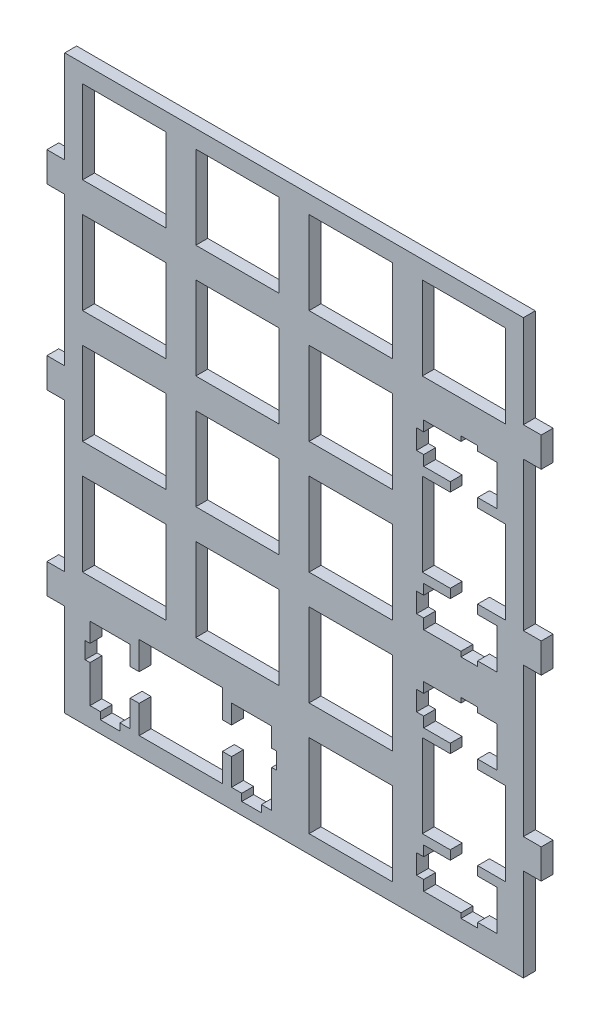
SolidWorks part; units mm, degrees
ref_plane "前视基准面" through (0, 0, 0) normal (0, 0, 1) x (1, 0, 0)
ref_plane "上视基准面" through (0, 0, 0) normal (0, 1, 0) x (1, 0, 0)
ref_plane "右视基准面" through (0, 0, 0) normal (1, 0, 0) x (0, 0, -1)
other "Configuration Table"
sketch "Model" plane through (0, 0, 0) normal (0, 0, 1) x (1, 0, 0)
  line L0 (12.1447, 16.7831) -> (12.1447, 12.0826)
  line L1 (12.1447, 12.0826) -> (10.6192, 12.0826)
  line L2 (10.6192, 12.0826) -> (10.6192, 15.3128)
  line L3 (10.6192, 15.3128) -> (3.8695, 15.3128)
  line L4 (3.8695, 15.3128) -> (3.8695, 12.0826)
  line L5 (3.8695, 12.0826) -> (3.0441, 12.0826)
  line L6 (3.0441, 12.0826) -> (3.0441, 9.2838)
  line L7 (3.0441, 9.2838) -> (3.8695, 9.2838)
  line L8 (3.8695, 9.2838) -> (3.8695, 3.0138)
  line L9 (3.8695, 3.0138) -> (5.5948, 3.0138)
  line L10 (5.5948, 3.0138) -> (5.5948, 1.8135)
  line L11 (5.5948, 1.8135) -> (8.8939, 1.8135)
  line L12 (8.8939, 1.8135) -> (8.8939, 3.0138)
  line L13 (8.8939, 3.0138) -> (10.6192, 3.0138)
  line L14 (10.6192, 3.0138) -> (10.6192, 7.4827)
  line L15 (10.6192, 7.4827) -> (12.1447, 7.4827)
  line L16 (12.1447, 7.4827) -> (12.1447, 2.7836)
  line L17 (12.1447, 2.7836) -> (26.1441, 2.7836)
  line L18 (26.1441, 2.7836) -> (26.1441, 7.4827)
  line L19 (26.1441, 7.4827) -> (27.6696, 7.4827)
  line L20 (27.6696, 7.4827) -> (27.6696, 3.0138)
  line L21 (27.6696, 3.0138) -> (29.3949, 3.0138)
  line L22 (29.3949, 3.0138) -> (29.3949, 1.8135)
  line L23 (29.3949, 1.8135) -> (32.694, 1.8135)
  line L24 (32.694, 1.8135) -> (32.694, 3.0138)
  line L25 (32.694, 3.0138) -> (34.4193, 3.0138)
  line L26 (34.4193, 3.0138) -> (34.4193, 9.2838)
  line L27 (34.4193, 9.2838) -> (35.2447, 9.2838)
  line L28 (35.2447, 9.2838) -> (35.2447, 12.0826)
  line L29 (35.2447, 12.0826) -> (34.4193, 12.0826)
  line L30 (34.4193, 12.0826) -> (34.4193, 15.3128)
  line L31 (34.4193, 15.3128) -> (27.6696, 15.3128)
  line L32 (27.6696, 15.3128) -> (27.6696, 12.0826)
  line L33 (27.6696, 12.0826) -> (26.1441, 12.0826)
  line L34 (26.1441, 12.0826) -> (26.1441, 16.7831)
  line L35 (26.1441, 16.7831) -> (12.1447, 16.7831)
  line L36 (40.7197, 16.7831) -> (54.719, 16.7831)
  line L37 (54.719, 16.7831) -> (54.719, 2.7836)
  line L38 (54.719, 2.7836) -> (40.7197, 2.7836)
  line L39 (40.7197, 2.7836) -> (40.7197, 16.7831)
  line L40 (66.27, 35.4087) -> (66.27, 34.5833)
  line L41 (66.27, 34.5833) -> (59.9997, 34.5833)
  line L42 (59.9997, 34.5833) -> (59.9997, 32.8579)
  line L43 (59.9997, 32.8579) -> (58.7996, 32.8579)
  line L44 (58.7996, 32.8579) -> (58.7996, 29.5589)
  line L45 (58.7996, 29.5589) -> (59.9997, 29.5589)
  line L46 (59.9997, 29.5589) -> (59.9997, 27.8336)
  line L47 (59.9997, 27.8336) -> (64.4701, 27.8336)
  line L48 (64.4701, 27.8336) -> (64.4701, 26.3081)
  line L49 (64.4701, 26.3081) -> (59.7697, 26.3081)
  line L50 (59.7697, 26.3081) -> (59.7697, 12.3086)
  line L51 (59.7697, 12.3086) -> (64.4701, 12.3086)
  line L52 (64.4701, 12.3086) -> (64.4701, 10.7831)
  line L53 (64.4701, 10.7831) -> (59.9997, 10.7831)
  line L54 (59.9997, 10.7831) -> (59.9997, 9.0579)
  line L55 (59.9997, 9.0579) -> (58.7996, 9.0579)
  line L56 (58.7996, 9.0579) -> (58.7996, 5.7588)
  line L57 (58.7996, 5.7588) -> (59.9997, 5.7588)
  line L58 (59.9997, 5.7588) -> (59.9997, 4.0335)
  line L59 (59.9997, 4.0335) -> (66.27, 4.0335)
  line L60 (66.27, 4.0335) -> (66.27, 3.2081)
  line L61 (66.27, 3.2081) -> (69.07, 3.2081)
  line L62 (69.07, 3.2081) -> (69.07, 4.0335)
  line L63 (69.07, 4.0335) -> (72.3, 4.0335)
  line L64 (72.3, 4.0335) -> (72.3, 10.7831)
  line L65 (72.3, 10.7831) -> (69.07, 10.7831)
  line L66 (69.07, 10.7831) -> (69.07, 12.3086)
  line L67 (69.07, 12.3086) -> (73.769, 12.3086)
  line L68 (73.769, 12.3086) -> (73.769, 26.3081)
  line L69 (73.769, 26.3081) -> (69.07, 26.3081)
  line L70 (69.07, 26.3081) -> (69.07, 27.8336)
  line L71 (69.07, 27.8336) -> (72.3, 27.8336)
  line L72 (72.3, 27.8336) -> (72.3, 34.5833)
  line L73 (72.3, 34.5833) -> (69.07, 34.5833)
  line L74 (69.07, 34.5833) -> (69.07, 35.4087)
  line L75 (69.07, 35.4087) -> (66.27, 35.4087)
  line L76 (2.6197, 35.833) -> (16.6192, 35.833)
  line L77 (16.6192, 35.833) -> (16.6192, 21.8336)
  line L78 (16.6192, 21.8336) -> (2.6197, 21.8336)
  line L79 (2.6197, 21.8336) -> (2.6197, 35.833)
  line L80 (21.6697, 35.833) -> (35.669, 35.833)
  line L81 (35.669, 35.833) -> (35.669, 21.8336)
  line L82 (35.669, 21.8336) -> (21.6697, 21.8336)
  line L83 (21.6697, 21.8336) -> (21.6697, 35.833)
  line L84 (40.7197, 35.833) -> (54.719, 35.833)
  line L85 (54.719, 35.833) -> (54.719, 21.8336)
  line L86 (54.719, 21.8336) -> (40.7197, 21.8336)
  line L87 (40.7197, 21.8336) -> (40.7197, 35.833)
  line L88 (2.6197, 54.8831) -> (16.6192, 54.8831)
  line L89 (16.6192, 54.8831) -> (16.6192, 40.8838)
  line L90 (16.6192, 40.8838) -> (2.6197, 40.8838)
  line L91 (2.6197, 40.8838) -> (2.6197, 54.8831)
  line L92 (21.6697, 54.8831) -> (35.669, 54.8831)
  line L93 (35.669, 54.8831) -> (35.669, 40.8838)
  line L94 (35.669, 40.8838) -> (21.6697, 40.8838)
  line L95 (21.6697, 40.8838) -> (21.6697, 54.8831)
  line L96 (40.7197, 54.8831) -> (54.719, 54.8831)
  line L97 (54.719, 54.8831) -> (54.719, 40.8838)
  line L98 (54.719, 40.8838) -> (40.7197, 40.8838)
  line L99 (40.7197, 40.8838) -> (40.7197, 54.8831)
  line L100 (66.27, 73.5087) -> (66.27, 72.6832)
  line L101 (66.27, 72.6832) -> (59.9997, 72.6832)
  line L102 (59.9997, 72.6832) -> (59.9997, 70.9581)
  line L103 (59.9997, 70.9581) -> (58.7996, 70.9581)
  line L104 (58.7996, 70.9581) -> (58.7996, 67.6589)
  line L105 (58.7996, 67.6589) -> (59.9997, 67.6589)
  line L106 (59.9997, 67.6589) -> (59.9997, 65.9335)
  line L107 (59.9997, 65.9335) -> (64.4701, 65.9335)
  line L108 (64.4701, 65.9335) -> (64.4701, 64.4081)
  line L109 (64.4701, 64.4081) -> (59.7697, 64.4081)
  line L110 (59.7697, 64.4081) -> (59.7697, 50.4088)
  line L111 (59.7697, 50.4088) -> (64.4701, 50.4088)
  line L112 (64.4701, 50.4088) -> (64.4701, 48.883)
  line L113 (64.4701, 48.883) -> (59.9997, 48.883)
  line L114 (59.9997, 48.883) -> (59.9997, 47.1579)
  line L115 (59.9997, 47.1579) -> (58.7996, 47.1579)
  line L116 (58.7996, 47.1579) -> (58.7996, 43.8587)
  line L117 (58.7996, 43.8587) -> (59.9997, 43.8587)
  line L118 (59.9997, 43.8587) -> (59.9997, 42.1337)
  line L119 (59.9997, 42.1337) -> (66.27, 42.1337)
  line L120 (66.27, 42.1337) -> (66.27, 41.3082)
  line L121 (66.27, 41.3082) -> (69.07, 41.3082)
  line L122 (69.07, 41.3082) -> (69.07, 42.1337)
  line L123 (69.07, 42.1337) -> (72.3, 42.1337)
  line L124 (72.3, 42.1337) -> (72.3, 48.883)
  line L125 (72.3, 48.883) -> (69.07, 48.883)
  line L126 (69.07, 48.883) -> (69.07, 50.4088)
  line L127 (69.07, 50.4088) -> (73.769, 50.4088)
  line L128 (73.769, 50.4088) -> (73.769, 64.4081)
  line L129 (73.769, 64.4081) -> (69.07, 64.4081)
  line L130 (69.07, 64.4081) -> (69.07, 65.9335)
  line L131 (69.07, 65.9335) -> (72.3, 65.9335)
  line L132 (72.3, 65.9335) -> (72.3, 72.6832)
  line L133 (72.3, 72.6832) -> (69.07, 72.6832)
  line L134 (69.07, 72.6832) -> (69.07, 73.5087)
  line L135 (69.07, 73.5087) -> (66.27, 73.5087)
  line L136 (2.6197, 73.9331) -> (16.6192, 73.9331)
  line L137 (16.6192, 73.9331) -> (16.6192, 59.9338)
  line L138 (16.6192, 59.9338) -> (2.6197, 59.9338)
  line L139 (2.6197, 59.9338) -> (2.6197, 73.9331)
  line L140 (21.6697, 73.9331) -> (35.669, 73.9331)
  line L141 (35.669, 73.9331) -> (35.669, 59.9338)
  line L142 (35.669, 59.9338) -> (21.6697, 59.9338)
  line L143 (21.6697, 59.9338) -> (21.6697, 73.9331)
  line L144 (40.7197, 73.9331) -> (54.719, 73.9331)
  line L145 (54.719, 73.9331) -> (54.719, 59.9338)
  line L146 (54.719, 59.9338) -> (40.7197, 59.9338)
  line L147 (40.7197, 59.9338) -> (40.7197, 73.9331)
  line L148 (2.6197, 92.9831) -> (16.6192, 92.9831)
  line L149 (16.6192, 92.9831) -> (16.6192, 78.9838)
  line L150 (16.6192, 78.9838) -> (2.6197, 78.9838)
  line L151 (2.6197, 78.9838) -> (2.6197, 92.9831)
  line L152 (21.6697, 92.9831) -> (35.669, 92.9831)
  line L153 (35.669, 92.9831) -> (35.669, 78.9838)
  line L154 (35.669, 78.9838) -> (21.6697, 78.9838)
  line L155 (21.6697, 78.9838) -> (21.6697, 92.9831)
  line L156 (40.7197, 92.9831) -> (54.719, 92.9831)
  line L157 (54.719, 92.9831) -> (54.719, 78.9838)
  line L158 (54.719, 78.9838) -> (40.7197, 78.9838)
  line L159 (40.7197, 78.9838) -> (40.7197, 92.9831)
  line L160 (59.7697, 92.9831) -> (73.769, 92.9831)
  line L161 (73.769, 92.9831) -> (73.769, 78.9838)
  line L162 (73.769, 78.9838) -> (59.7697, 78.9838)
  line L163 (59.7697, 78.9838) -> (59.7697, 92.9831)
  line L164 (-0.3804, 95.9831) -> (76.769, 95.9831)
  line L165 (-0.3804, -0.2164) -> (-0.3803, 15.3834)
  line L166 (-0.3804, -0.2164) -> (76.769, -0.2164)
  line L167 (76.769, -0.2164) -> (76.769, 15.3834)
  line L168 (38.1943, 95.9831) -> (38.1943, -0.2164) construction
  line L169 (-0.3804, 47.8834) -> (76.769, 47.8834) construction
  line L170 (-0.3804, 50.3834) -> (-3.3804, 50.3834)
  line L171 (-0.3804, 45.3834) -> (-3.3804, 45.3834)
  line L172 (-3.3804, 50.3834) -> (-3.3804, 45.3834)
  line L173 (-0.3804, 80.3834) -> (-3.3804, 80.3834)
  line L174 (-0.3804, 75.3834) -> (-3.3804, 75.3834)
  line L175 (-3.3804, 80.3834) -> (-3.3804, 75.3834)
  line L176 (-0.3803, 20.3834) -> (-3.3803, 20.3834)
  line L177 (-0.3803, 15.3834) -> (-3.3803, 15.3834)
  line L178 (-3.3803, 20.3834) -> (-3.3803, 15.3834)
  line L179 (79.769, 20.3834) -> (79.769, 15.3834)
  line L180 (76.769, 15.3834) -> (79.769, 15.3834)
  line L181 (76.769, 20.3834) -> (79.769, 20.3834)
  line L182 (79.769, 80.3834) -> (79.769, 75.3834)
  line L183 (76.769, 75.3834) -> (79.769, 75.3834)
  line L184 (76.769, 80.3834) -> (79.769, 80.3834)
  line L185 (79.769, 50.3834) -> (79.769, 45.3834)
  line L186 (76.769, 45.3834) -> (79.769, 45.3834)
  line L187 (76.769, 50.3834) -> (79.769, 50.3834)
  line L188 (-0.3804, 80.3834) -> (-0.3804, 95.9831)
  line L189 (76.769, 80.3834) -> (76.769, 95.9831)
  line L190 (76.769, 20.3834) -> (76.769, 45.3834)
  line L191 (-0.3803, 20.3834) -> (-0.3804, 45.3834)
  line L192 (-0.3804, 50.3834) -> (-0.3804, 75.3834)
  line L193 (76.769, 50.3834) -> (76.769, 75.3834)
  dimension "D1" = 77.1493
  dimension "D2" = 96.1995
  dimension "D3" = 3
  dimension "D4" = 3
  dimension "D5" = 2.5
  dimension "D6" = 2.5
  dimension "D7" = 2
  dimension "D8" = 2
extrude "凸台-拉伸1" add sketch "Model" along normal blind 2
